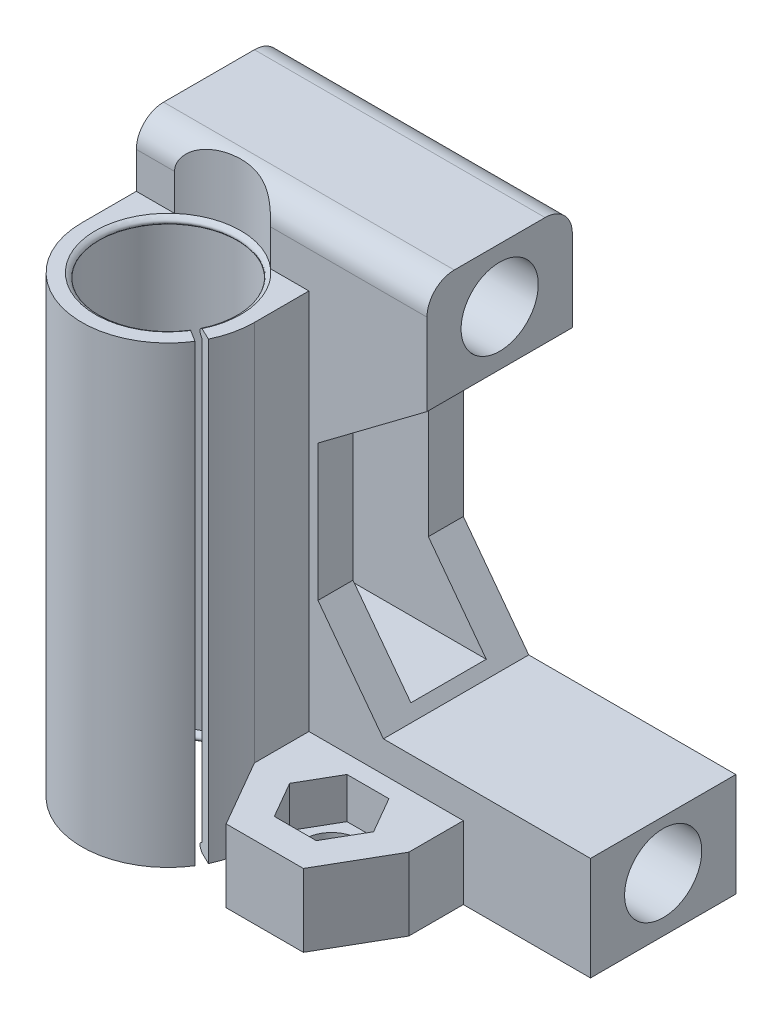
SolidWorks part; units mm, degrees
ref_plane "Plan de face" through (0, 0, 0) normal (0, 0, 1) x (1, 0, 0)
ref_plane "Plan de dessus" through (0, 0, 0) normal (0, 1, 0) x (1, 0, 0)
ref_plane "Plan de droite" through (0, 0, 0) normal (1, 0, 0) x (0, 0, -1)
sketch "Esquisse1" plane through (0, 0, 0) normal (0, 0, 1) x (1, 0, 0)
  line L0 (0, 0) -> (0, 57)
  line L1 (0, 57) -> (32, 57)
  line L2 (32, 57) -> (32, 45)
  line L3 (32, 45) -> (20, 36)
  line L4 (20, 36) -> (20, 21)
  line L5 (20, 21) -> (27.2, 11.4)
  line L6 (27.2, 11.4) -> (50, 11.4)
  line L7 (50, 11.4) -> (50, 0)
  line L8 (50, 0) -> (0, 0)
  dimension "D1" = 57
  dimension "D2" = 32
  dimension "D3" = 12
  dimension "D4" = 20
  dimension "D5" = 50
  dimension "D6" = 15
  dimension "D7" = 15
  dimension "D8" = 12
extrude "Boss.-Extru.1" add sketch "Esquisse1" along normal blind 16
fillet "Congé1" radius 3 2 edges at (16, 57, 16) (16, 57, 0)
sketch "Esquisse2" plane through (0, 0, 0) normal (-1, 0, 0) x (0, 0, 1)
  line L0 (8, 57) -> (8, 0) construction
  line L1 (13, 57) -> (3, 57) construction
  line L2 (16, 0) -> (0, 0) construction
  line L3 (3.85, 42.5) -> (5.85, 44.5)
  line L4 (5.85, 44.5) -> (10.15, 44.5)
  line L5 (3.85, 42.5) -> (3.85, 12.5)
  line L6 (3.85, 12.5) -> (12.15, 12.5)
  line L7 (12.15, 42.5) -> (12.15, 12.5)
  line L8 (3.85, 44.5) -> (12.15, 12.5) construction
  line L9 (3.85, 12.5) -> (12.15, 44.5) construction
  line L10 (10.15, 44.5) -> (12.15, 42.5)
  circle A0 centre (8, 51) radius 4.25
  circle A1 centre (8, 6) radius 4.25
  point P10 (8, 28.5)
  dimension "D2" = 8.5
  dimension "D1" = 45
  dimension "D3" = 6
  dimension "D4" = 32
  dimension "D5" = 8.3
extrude "Enlèv. mat.-Extru.1" cut sketch "Esquisse2" against normal through all
ref_plane "Plan1" through (0, 50, 0) normal (0, 1, 0) x (1, 0, 0)
sketch "Esquisse3" plane through (0, 50, 0) normal (0, 1, 0) x (1, 0, 0)
  line L0 (0, 0) -> (32, 0) construction
  line L2 (0, 0) -> (0, -29.7367) construction
  line L3 (16.7071, -25.4724) -> (18.8974, -26.5276)
  line L4 (18.8974, -26.5276) -> (18.3765, -27.6087)
  line L5 (18.3765, -27.6087) -> (16.2631, -26.2733)
  line L6 (17.8022, -26) -> (17.8022, -16) construction
  line L7 (32, -16) -> (0, -16) construction
  arc A0 (16.7071, -25.4724) -> (16.2631, -26.2733) centre (9.5, -22) ccw
  dimension "D2" = 16
  dimension "D1" = 22
  dimension "D3" = 9.5
  dimension "D4" = 10
  dimension "D5" = 1.2
  dimension "D6" = 2.5
sketch "Esquisse4" plane through (0, 50, 0) normal (0, 1, 0) x (1, 0, 0)
  line L2 (0, -22) -> (0, -16)
  line L3 (19, -22) -> (19, -16)
  line L4 (0, -16) -> (19, -16)
  line L5 (0, -16) -> (0, -35.918) construction
  arc A0 (0, -22) -> (19, -22) centre (9.5, -22) ccw
  dimension "D1" = 9.5
  dimension "D2" = 22
extrude "Boss.-Extru.3" add sketch "Esquisse4" against normal blind 50
extrude "Enlèv. mat.-Extru.3" cut sketch "Esquisse3" against normal through all both and the other way through all
sketch "Esquisse7" plane through (0, 0, 0) normal (0, -1, 0) x (1, 0, 0)
  line L0 (27.5, 22) -> (36, 22) construction
  line L1 (36, 22) -> (31.75, 29.3612)
  line L2 (31.75, 29.3612) -> (23.25, 29.3612)
  line L3 (23.25, 29.3612) -> (19, 22)
  line L4 (19, 22) -> (23.25, 14.6388)
  line L5 (23.25, 14.6388) -> (31.75, 14.6388)
  line L6 (31.75, 14.6388) -> (36, 22)
  line L7 (19, 16) -> (50, 16) construction
  line L8 (19, 22) -> (19, 14.6388)
  line L9 (19, 14.6388) -> (23.25, 14.6388)
  line L10 (36, 22) -> (36, 14.6388)
  line L11 (36, 14.6388) -> (31.75, 14.6388)
  circle A0 centre (27.5, 22) radius 7.3612 construction
  arc M1 (19, 22) -> (18.0585, 26.1234) centre (9.5, 22) ccw
  line M9 (50, 16) -> (19, 16)
  line M10 (19, 16) -> (19, 22)
  dimension "D1" = 17
  dimension "D2" = 6
  dimension "D3" = 14
extrude "Boss.-Extru.4" add sketch "Esquisse7" against normal blind 8 contours L6 L1 L2 L3 L4 M9 M1 M10 | L4 M10 M9 | L10 L6 M9
sketch "Esquisse8" plane through (0, 8, 0) normal (0, 1, 0) x (1, 0, 0)
  line L0 (27.5, -22) -> (32.1188, -22) construction
  line L1 (32.1188, -22) -> (29.8094, -18)
  line L2 (29.8094, -18) -> (25.1906, -18)
  line L3 (25.1906, -18) -> (22.8812, -22)
  line L4 (22.8812, -22) -> (25.1906, -26)
  line L5 (25.1906, -26) -> (29.8094, -26)
  line L6 (29.8094, -26) -> (32.1188, -22)
  line L7 (27.5, -29.3612) -> (27.5, -22) construction
  line L8 (31.75, -29.3612) -> (23.25, -29.3612) construction
  line L9 (27.5, -22) -> (36, -22) construction
  circle A0 centre (27.5, -22) radius 4 construction
  dimension "D1" = 8
extrude "Enlèv. mat.-Extru.5" cut sketch "Esquisse8" against normal blind 4.5
sketch "Esquisse10" plane through (0, 3.5, 0) normal (0, 1, 0) x (1, 0, 0)
  line L0 (27.5, -22) -> (27.5, -29.3612) construction
  line L1 (31.75, -29.3612) -> (23.25, -29.3612) construction
  line L2 (27.5, -22) -> (36, -22) construction
  circle A0 centre (27.5, -22) radius 3
  dimension "D1" = 6
extrude "Enlèv. mat.-Extru.6" cut sketch "Esquisse10" against normal through all
ref_plane "Plan2" through (9, 0, 0) normal (-1, 0, 0) x (0, 0, 1)
sketch "Esquisse11" plane through (-7.2239, 0, 11.4328) normal (0.5342, 0, -0.8454) x (-0.8454, 0, -0.5342)
  line L0 (-27.7827, 0) -> (-27.7827, 50) construction
  line L1 (-27.7827, 50) -> (-27.7827, 49)
  line L2 (-27.2827, 49.5) -> (-27.7827, 49.5) construction
  line L3 (-27.2827, 49.5) -> (-27.7827, 50) construction
  line L4 (-27.7827, 0) -> (-27.7827, 1)
  line L5 (-27.7827, 0.5) -> (-27.2827, 0.5) construction
  line L6 (-27.2827, 0.5) -> (-27.7827, 1) construction
  spline S0 degree 2 poles (-27.7827, 50) (-26.7827, 49.5) (-27.7827, 49) knots 0 0 0 1 1 1
  spline S1 degree 2 poles (-27.7827, 0) (-26.7827, 0.5) (-27.7827, 1) knots 0 0 0 1 1 1
  dimension "D1" = 0.5
  dimension "D2" = 1
  dimension "D3" = 1
  dimension "D4" = 0.5
sweep "Balayage1" add profiles "Esquisse11" path edge at (2.5034, 0, 18.1208)
